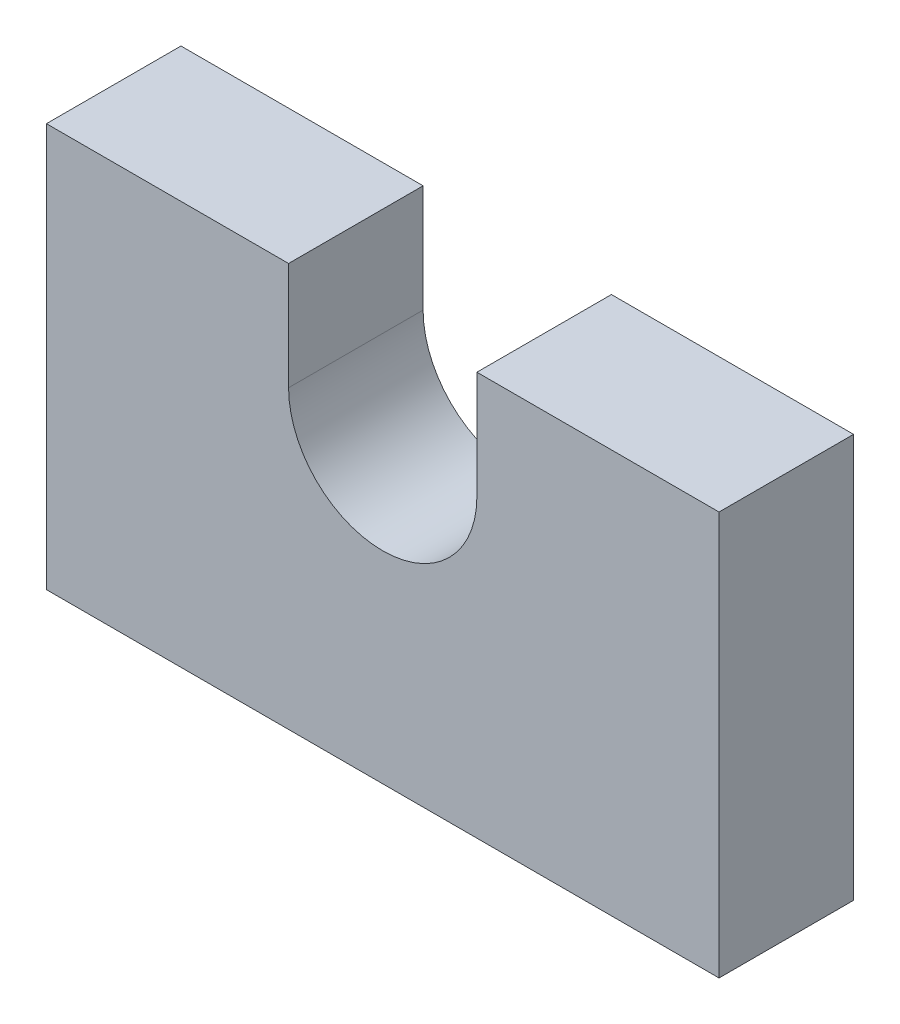
SolidWorks part; units mm, degrees
material "Plain Carbon Steel"
ref_plane "Front Plane" through (0, 0, 0) normal (0, 0, 1) x (1, 0, 0)
ref_plane "Top Plane" through (0, 0, 0) normal (0, 1, 0) x (1, 0, 0)
ref_plane "Right Plane" through (0, 0, 0) normal (1, 0, 0) x (0, 0, -1)
sketch "Sketch3" plane through (0, 0, 0) normal (0, 0, 1) x (1, 0, 0)
  line L0 (-125, 0) -> (125, 0)
  line L1 (-125, 0) -> (-125, 150)
  line L2 (125, 0) -> (125, 150)
  line L3 (-125, 150) -> (-35, 150)
  line L4 (125, 150) -> (35, 150)
  line L5 (-35, 150) -> (-35, 110)
  line L6 (35, 150) -> (35, 110)
  arc A0 (-35, 110) -> (35, 110) centre (0, 110) ccw
  dimension "D4" = 0
  dimension "D1" = 0
  dimension "D2" = 0
extrude "Boss-Extrude1" add sketch "Sketch3" along normal blind 0 separate body
